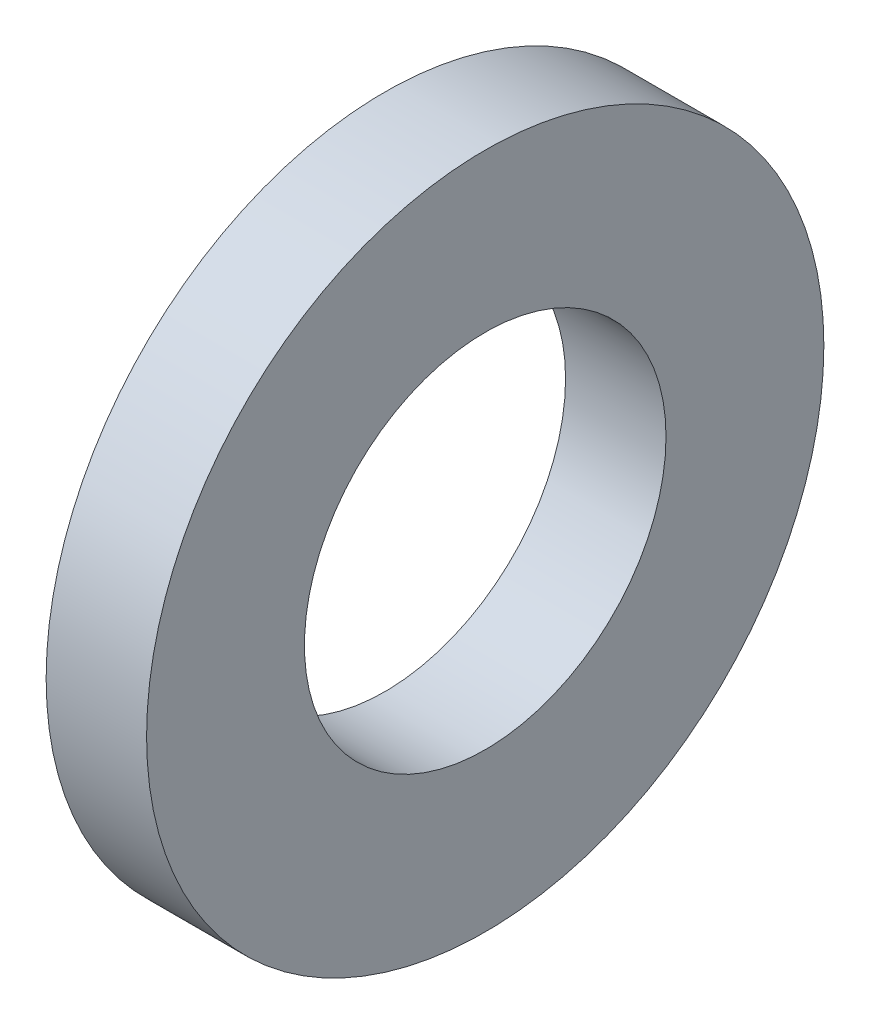
SolidWorks part; units mm, degrees
ref_plane "Front Plane" through (0, 0, 0) normal (0, 0, 1) x (1, 0, 0)
ref_plane "Top Plane" through (0, 0, 0) normal (0, 1, 0) x (1, 0, 0)
ref_plane "Right Plane" through (0, 0, 0) normal (1, 0, 0) x (0, 0, -1)
sketch "Sketch1" plane through (0, 0, 0) normal (1, 0, 0) x (0, 0, -1)
  circle A0 centre (0, 0) radius 5.9944
  circle A1 centre (0, 0) radius 3.2004
  dimension "OD" = 11.9888
  dimension "ID" = 6.4008
extrude "Boss-Extrude1" add sketch "Sketch1" along normal blind 1.778
